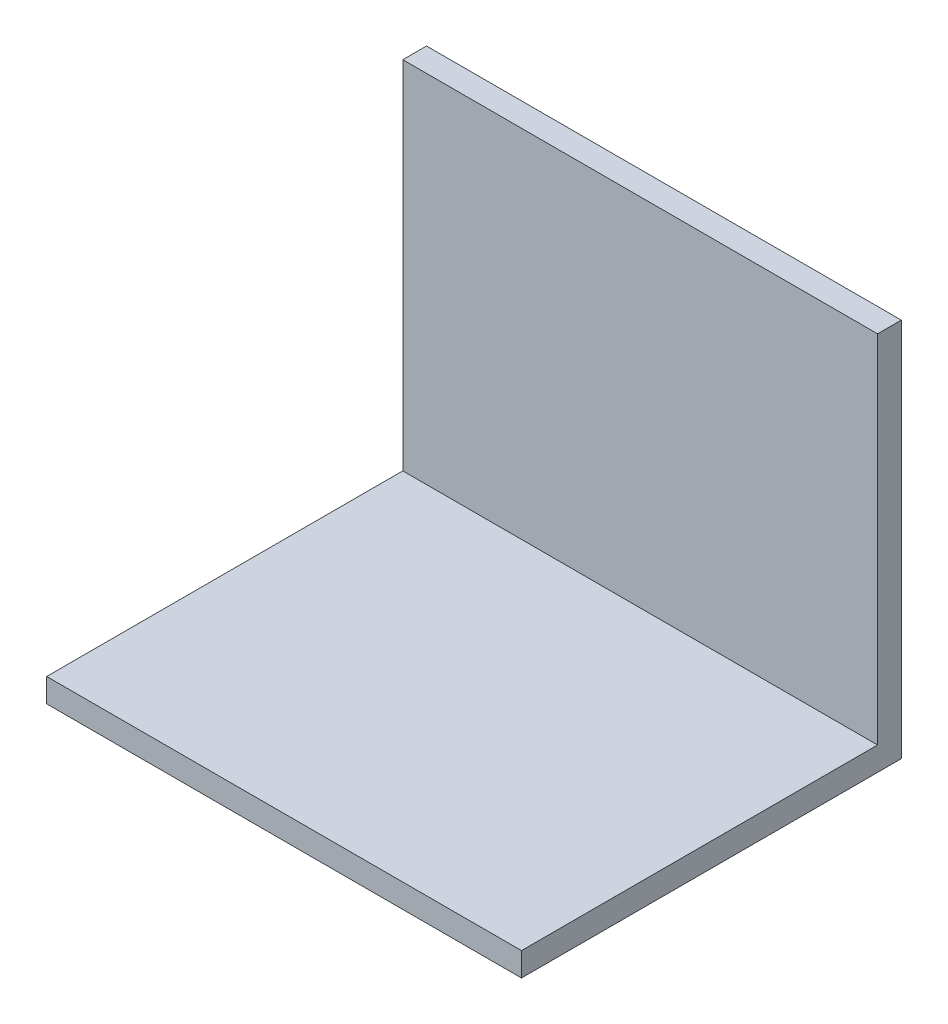
SolidWorks part; units mm, degrees
ref_plane "Front Plane" through (0, 0, 0) normal (0, 0, 1) x (1, 0, 0)
ref_plane "Top Plane" through (0, 0, 0) normal (0, 1, 0) x (1, 0, 0)
ref_plane "Right Plane" through (0, 0, 0) normal (1, 0, 0) x (0, 0, -1)
sketch "Sketch2" plane through (0, 0, 0) normal (1, 0, 0) x (0, 0, -1)
  line L9 (0, 0) -> (-101.6, 0)
  line L11 (-6.35, 6.35) -> (-101.6, 6.35)
  line L12 (-101.6, 0) -> (-101.6, 6.35)
  line L14 (0, 0) -> (0, 101.6)
  line L15 (0, 101.6) -> (-6.35, 101.6)
  line L16 (-6.35, 6.35) -> (-6.35, 101.6)
  dimension "D1" = 6.35
  dimension "D2" = 101.6
  dimension "D3" = 101.6
extrude "Boss-Extrude1" add sketch "Sketch2" along normal blind 127
sketch "Sketch3" plane through (0, 0, 6.35) normal (0, 0, 1) x (1, 0, 0)
  line L0 (127, 101.6) -> (0, 101.6) construction
  line L1 (0, 101.6) -> (0, 6.35) construction
  circle A0 centre (63.5, 53.975) radius 6.35
  point P5 (63.5, 101.6)
  point P9 (0, 53.975)
  dimension "D1" = 12.7
sketch "Sketch4" plane through (0, 6.35, 0) normal (0, 1, 0) x (1, 0, 0)
  line L0 (127, -101.6) -> (0, -101.6) construction
  line L1 (0, -6.35) -> (0, -101.6) construction
  circle A0 centre (63.5, -53.975) radius 6.35
  point P5 (63.5, -101.6)
  point P9 (0, -53.975)
  dimension "D1" = 12.7
